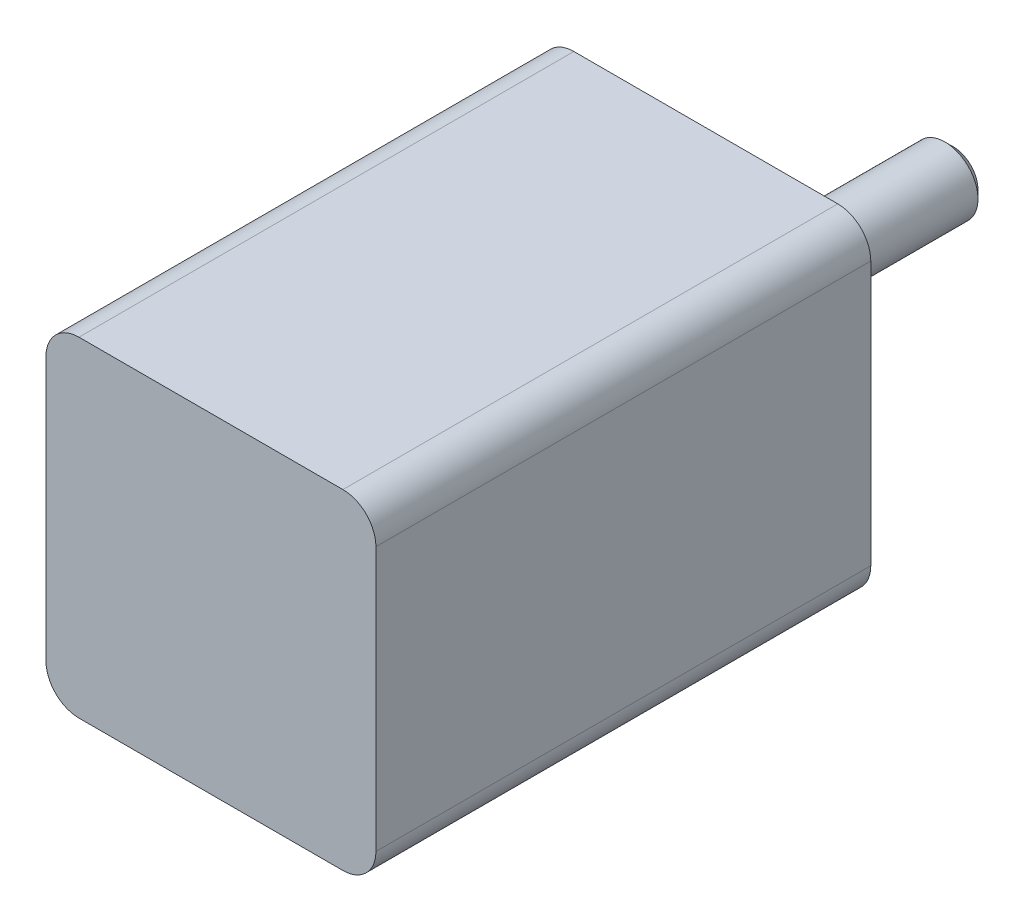
SolidWorks part; units mm, degrees
ref_plane "Front Plane" through (0, 0, 0) normal (0, 0, 1) x (1, 0, 0)
ref_plane "Top Plane" through (0, 0, 0) normal (0, 1, 0) x (1, 0, 0)
ref_plane "Right Plane" through (0, 0, 0) normal (1, 0, 0) x (0, 0, -1)
sketch "Sketch1" plane through (0, 0, 0) normal (0, 0, 1) x (1, 0, 0)
  line L1 (-10, 10) -> (10, 10)
  line L2 (-10, 10) -> (-10, -10)
  line L3 (-10, -10) -> (10, -10)
  line L4 (10, 10) -> (10, -10)
  line L5 (-10, 10) -> (10, -10) construction
  line L6 (-10, -10) -> (10, 10) construction
  point P0 (0, 0)
  dimension "D1" = 20
  dimension "D2" = 20
extrude "Boss-Extrude1" add sketch "Sketch1" along normal blind 30
sketch "Sketch2" plane through (0, 0, 0) normal (0, 0, -1) x (-1, 0, 0)
  circle A0 centre (0, 0) radius 7.5
  dimension "D1" = 15
extrude "Boss-Extrude2" add sketch "Sketch2" along normal blind 1.5
sketch "Sketch3" plane through (0, 0, -1.5) normal (0, 0, -1) x (-1, 0, 0)
  circle A0 centre (0, 0) radius 2
  dimension "D1" = 4
extrude "Boss-Extrude3" add sketch "Sketch3" along normal blind 13.5
hole_wizard "M2x0.4 Tapped Hole1" positions "Sketch4" profile "Sketch5" tap size "M2x0.4" standard "ANSI Metric"
sketch "Sketch4" plane through (0, 0, 0) normal (0, 0, -1) x (-1, 0, 0)
  line L0 (-8, 8) -> (8, -8) construction
  line L3 (-8, -8) -> (8, 8) construction
  point P0 (-8, 8)
  point P2 (8, 8)
  point P4 (8, -8)
  point P6 (-8, -8)
  point P19 (0, 0)
  point P20 (0, 0)
  dimension "D1" = 16
  dimension "D2" = 16
sketch "Sketch5" plane through (8, 8, 0) normal (1, 0, 0) x (0, 1, 0)
  line L0 (0, 0) -> (0, 3.9807)
  line L1 (0, 3.9807) -> (0.8, 3.5)
  line L2 (0.8, 3.5) -> (0.8, 0)
  line L5 (0.8, 0) -> (0, 0)
  line L10 (0, 3.9807) -> (-0.8, 3.5) construction
  line L11 (0, -6.35) -> (0, 107.95) construction
  dimension "Tap Drill Dia." = 1.6
  dimension "Tap Drill Depth" = 3.5
  dimension "Drill Angle" = 118
cosmetic thread "Hole Thread1" parameters "D1"=3.5, "D2"=2
cosmetic thread "Hole Thread2" parameters "D1"=3.5, "D2"=2
cosmetic thread "Hole Thread3" parameters "D1"=3.5, "D2"=2
cosmetic thread "Hole Thread4" parameters "D1"=3.5, "D2"=2
fillet "Fillet1" radius 2 4 edges at (-10, -10, 15) (10, -10, 15) (-10, 10, 15) (10, 10, 15)
chamfer "Chamfer1" distance 0.5 angle 45 1 edges at (-2, 0, -15)
